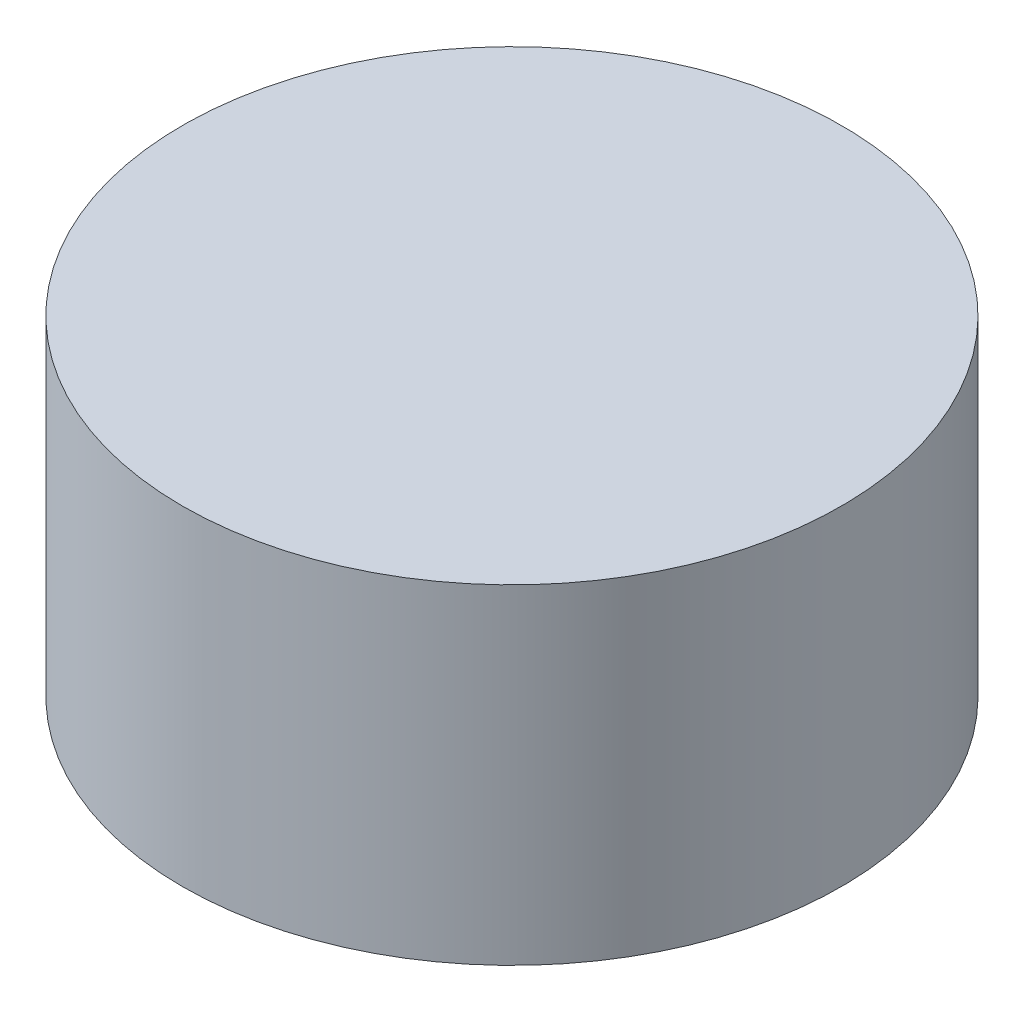
SolidWorks part; units mm, degrees
ref_plane "Front Plane" through (0, 0, 0) normal (0, 0, 1) x (1, 0, 0)
ref_plane "Top Plane" through (0, 0, 0) normal (0, 1, 0) x (1, 0, 0)
ref_plane "Right Plane" through (0, 0, 0) normal (1, 0, 0) x (0, 0, -1)
sketch "Sketch1" plane through (0, 0, 0) normal (0, 1, 0) x (1, 0, 0)
  circle A0 centre (-23.8809, 21.8524) radius 2.5
  point P2 (0, 0)
  dimension "D1" = 5
extrude "Boss-Extrude1" add sketch "Sketch1" along normal blind 2.5
